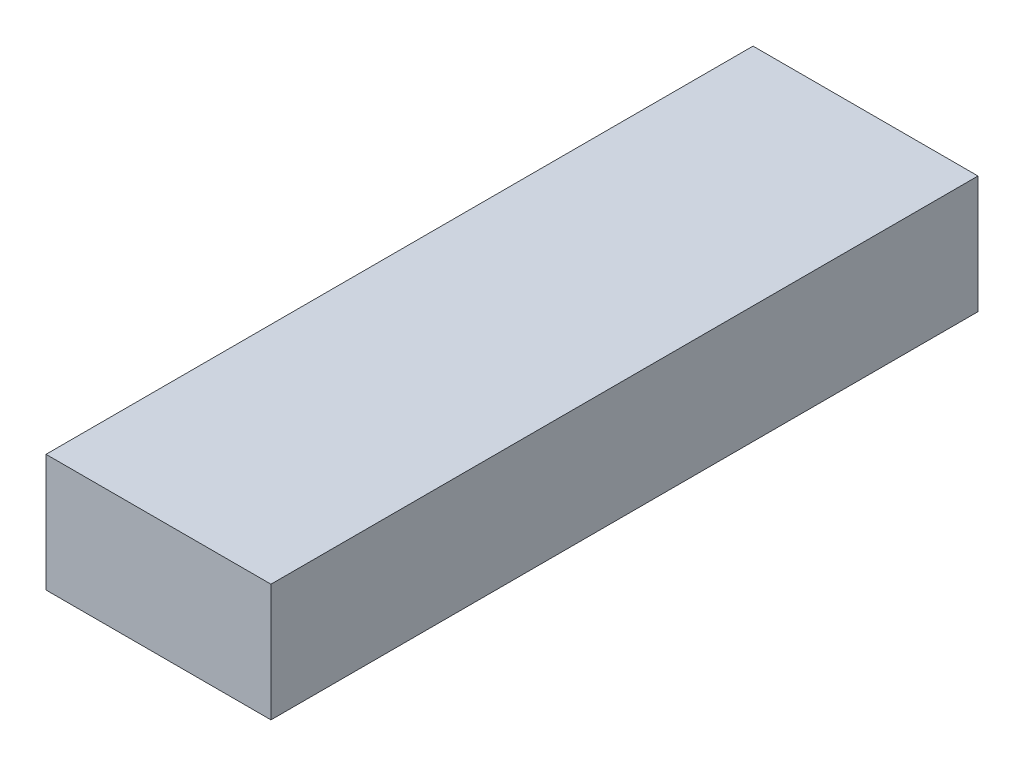
SolidWorks part; units mm, degrees
material "Sheet Moulding Compound"
ref_plane "Front Plane" through (0, 0, 0) normal (0, 0, 1) x (1, 0, 0)
ref_plane "Top Plane" through (0, 0, 0) normal (0, 1, 0) x (1, 0, 0)
ref_plane "Right Plane" through (0, 0, 0) normal (1, 0, 0) x (0, 0, -1)
sketch "Sketch1" plane through (0, 0, 0) normal (0, 0, 1) x (1, 0, 0)
  line L1 (-24.5, -12.8) -> (24.5, -12.8)
  line L2 (-24.5, -12.8) -> (-24.5, 12.8)
  line L3 (-24.5, 12.8) -> (24.5, 12.8)
  line L4 (24.5, -12.8) -> (24.5, 12.8)
  line L5 (-24.5, -12.8) -> (24.5, 12.8) construction
  line L6 (-24.5, 12.8) -> (24.5, -12.8) construction
  point P0 (0, 0)
  dimension "D1" = 49
  dimension "D2" = 25.6
extrude "Boss-Extrude1" add sketch "Sketch1" along normal blind 154
